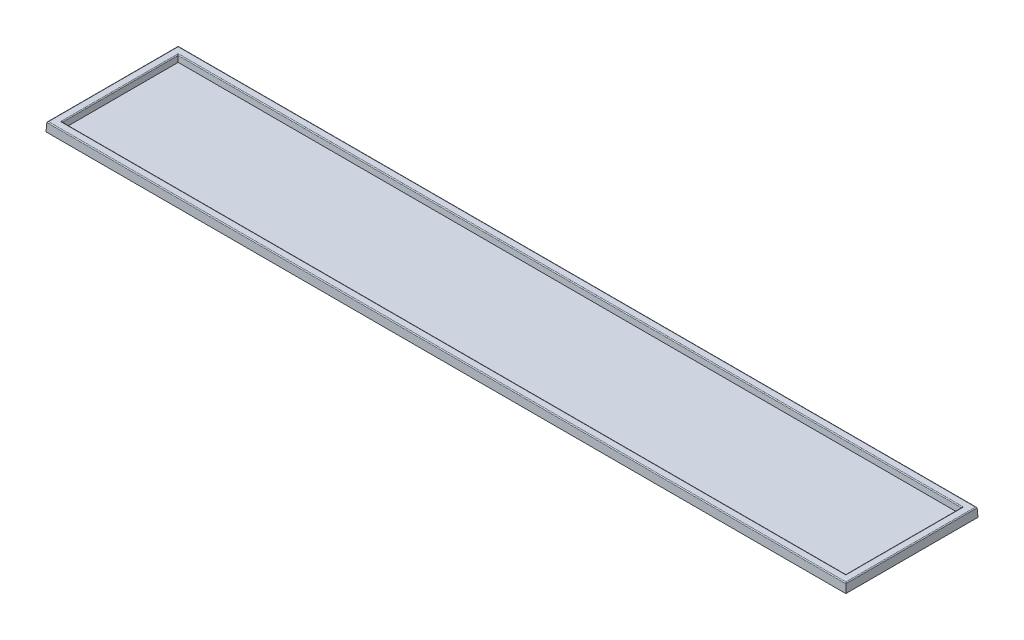
SolidWorks part; units mm, degrees
ref_plane "Front Plane" through (0, 0, 0) normal (0, 0, 1) x (1, 0, 0)
ref_plane "Top Plane" through (0, 0, 0) normal (0, 1, 0) x (1, 0, 0)
ref_plane "Right Plane" through (0, 0, 0) normal (1, 0, 0) x (0, 0, -1)
sketch "Sketch1" plane through (0, 0, 0) normal (0, 1, 0) x (1, 0, 0)
  line L1 (-449.25, -74.25) -> (449.25, -74.25)
  line L2 (-449.25, -74.25) -> (-449.25, 74.25)
  line L3 (-449.25, 74.25) -> (449.25, 74.25)
  line L4 (449.25, -74.25) -> (449.25, 74.25)
  line L5 (-449.25, -74.25) -> (449.25, 74.25) construction
  line L6 (-449.25, 74.25) -> (449.25, -74.25) construction
  point P0 (0, 0)
  dimension "D1" = 148.5
  dimension "D2" = 898.5
extrude "Boss-Extrude1" add sketch "Sketch1" along normal blind 10 draft 3
sketch "Sketch2" plane through (0, 10, 0) normal (0, 1, 0) x (1, 0, 0)
  line L0 (448.7259, 73.7259) -> (-448.7259, 73.7259) construction
  line L1 (-440.2259, -65.2259) -> (440.2259, -65.2259)
  line L2 (-440.2259, -65.2259) -> (-440.2259, 65.2259)
  line L3 (-440.2259, 65.2259) -> (440.2259, 65.2259)
  line L4 (440.2259, -65.2259) -> (440.2259, 65.2259)
  line L5 (-440.2259, -65.2259) -> (440.2259, 65.2259) construction
  line L6 (-440.2259, 65.2259) -> (440.2259, -65.2259) construction
  line L7 (448.7259, -73.7259) -> (448.7259, 73.7259) construction
  point P0 (0, 0)
  dimension "D1" = 8.5
  dimension "D2" = 8.5
extrude "Cut-Extrude1" cut sketch "Sketch2" against normal blind 7 draft 5
fillet "Fillet1" radius 1 8 edges at (0, 10, 73.7259) (-448.7259, 10, 0) (0, 10, -73.7259) (448.7259, 10, 0) (-440.2259, 10, 0) (0, 10, 65.2259) (440.2259, 10, 0) (0, 10, -65.2259)
